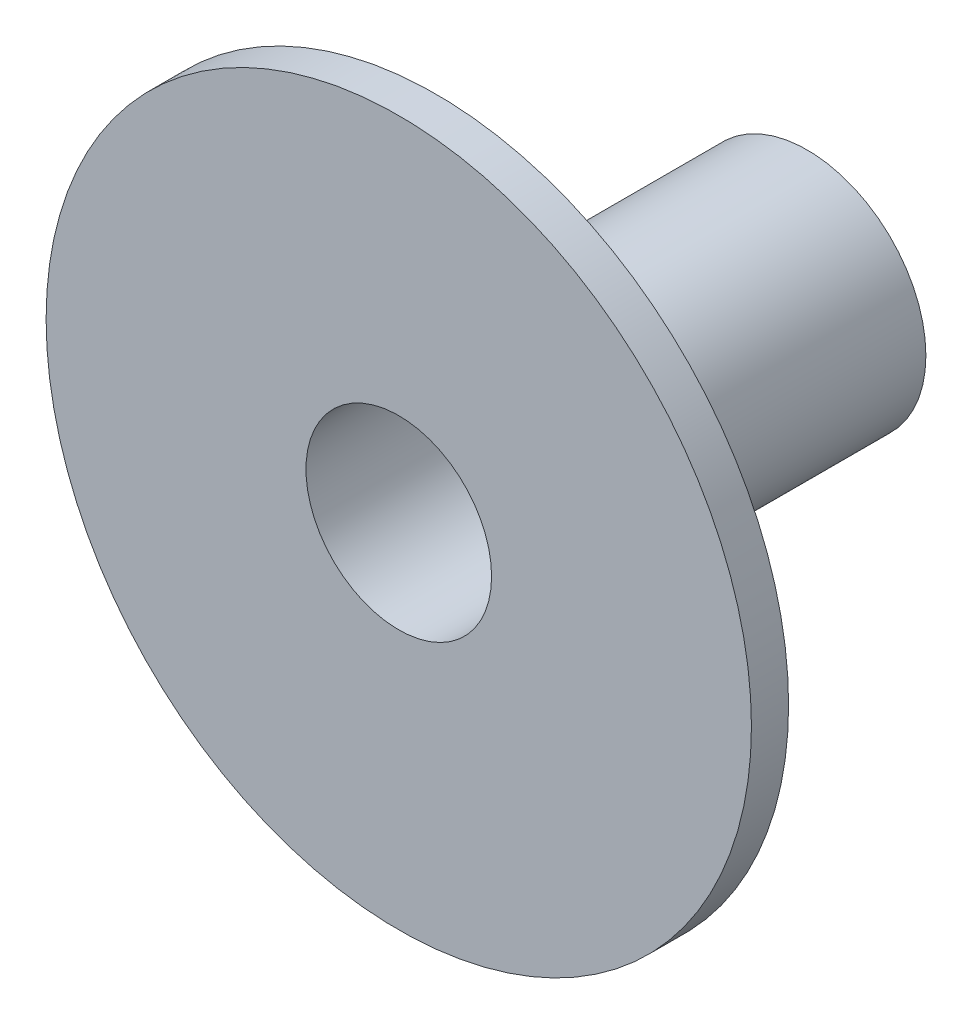
SolidWorks part; units mm, degrees
ref_plane "Front Plane" through (0, 0, 0) normal (0, 0, 1) x (1, 0, 0)
ref_plane "Top Plane" through (0, 0, 0) normal (0, 1, 0) x (1, 0, 0)
ref_plane "Right Plane" through (0, 0, 0) normal (1, 0, 0) x (0, 0, -1)
sketch "Sketch2" plane through (0, 0, 0) normal (1, 0, 0) x (0, 0, -1)
  line L0 (0, 0) -> (0, 9.4996)
  line L1 (0, 9.4996) -> (1.0008, 9.4996)
  line L2 (1.0008, 9.4996) -> (1.0008, 0)
  line L3 (0, 9.4996) -> (0, 2.4996)
  line L4 (1.0008, 0) -> (0, 0)
revolve "Revolve1" add sketch "Sketch2" angle 360 about L4
sketch "Sketch3" plane through (0, 0, 0) normal (0, 0, 1) x (1, 0, 0)
  circle A0 centre (0, 0) radius 2.5
extrude "Cut-Extrude1" cut sketch "Sketch3" against normal blind 2.54
sketch "Sketch4" plane through (0, 0, -1.0008) normal (0, 0, -1) x (-1, 0, 0)
  circle A0 centre (0, 0) radius 2.5
  circle A1 centre (0, 0) radius 3.1979
extrude "Boss-Extrude1" add sketch "Sketch4" along normal blind 10
